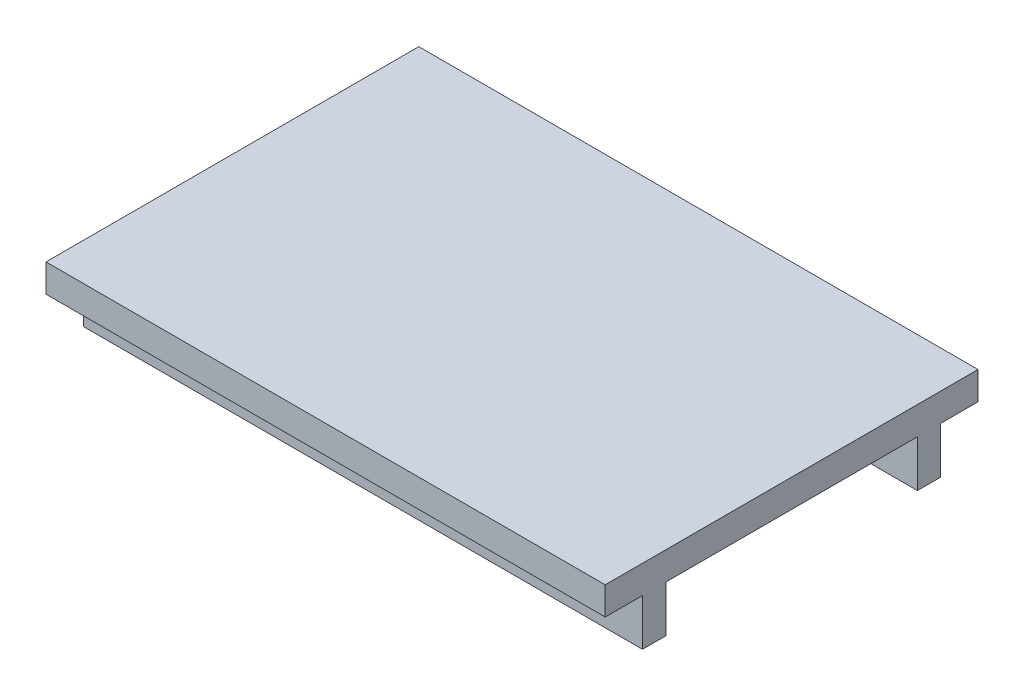
SolidWorks part; units mm, degrees
ref_plane "前基準面" through (0, 0, 0) normal (0, 0, 1) x (1, 0, 0)
ref_plane "上基準面" through (0, 0, 0) normal (0, 1, 0) x (1, 0, 0)
ref_plane "右基準面" through (0, 0, 0) normal (1, 0, 0) x (0, 0, -1)
sketch "草圖1" plane through (0, 0, 0) normal (0, 1, 0) x (1, 0, 0)
  line L1 (-60, -40) -> (60, -40)
  line L2 (-60, -40) -> (-60, 40)
  line L3 (-60, 40) -> (60, 40)
  line L4 (60, -40) -> (60, 40)
  line L5 (-60, -40) -> (60, 40) construction
  line L6 (-60, 40) -> (60, -40) construction
  point P0 (0, 0)
  dimension "D1" = 120
  dimension "D2" = 80
extrude "填料-伸長1" add sketch "草圖1" along normal blind 6
sketch3d "3D草圖3" plane through (0, 0, 0) normal (0, 0, 1) x (1, 0, 0)
  dimension "D1" = 20
sketch "草圖10" plane through (0, 0, 0) normal (0, -1, 0) x (1, 0, 0)
  line L0 (-60, -40) -> (-60, 40) construction
  line L1 (-60, 32) -> (60, 32)
  line L2 (-60, 32) -> (-60, 27)
  line L3 (-60, 27) -> (60, 27)
  line L4 (60, 32) -> (60, 27)
  line L5 (60, 40) -> (60, -40) construction
  line L6 (3.3, 20) -> (-3.3, 20) construction
  dimension "D1" = 5
  dimension "D2" = 12
extrude "填料-伸長3" add sketch "草圖10" along normal blind 10
sketch "草圖11" plane through (0, 0, 32) normal (0, 0, 1) x (1, 0, 0)
  line L0 (-20, -5) -> (50, -5) construction
  line L1 (-20, -2.5) -> (50, -2.5)
  line L2 (-20, -7.5) -> (50, -7.5)
  line L3 (-60, -10) -> (-60, 0) construction
  line L4 (60, -10) -> (-60, -10) construction
  line L6 (60, -10) -> (60, 0) construction
  circle A0 centre (-45, -5) radius 2.5
  arc A1 (-20, -2.5) -> (-20, -7.5) centre (-20, -5) ccw
  arc A2 (50, -7.5) -> (50, -2.5) centre (50, -5) ccw
  point P4 (15, -5)
  dimension "D2" = 5
  dimension "D3" = 2.5
  dimension "D1" = 15
  dimension "D4" = 5
  dimension "D5" = 70
  dimension "D6" = 10
extrude "除料-伸長1" cut sketch "草圖11" against normal up to next (5 mm away)
mirror "鏡射3" about plane through (0, 0, 0) normal (0, 0, 1) of "除料-伸長1", "填料-伸長3"
